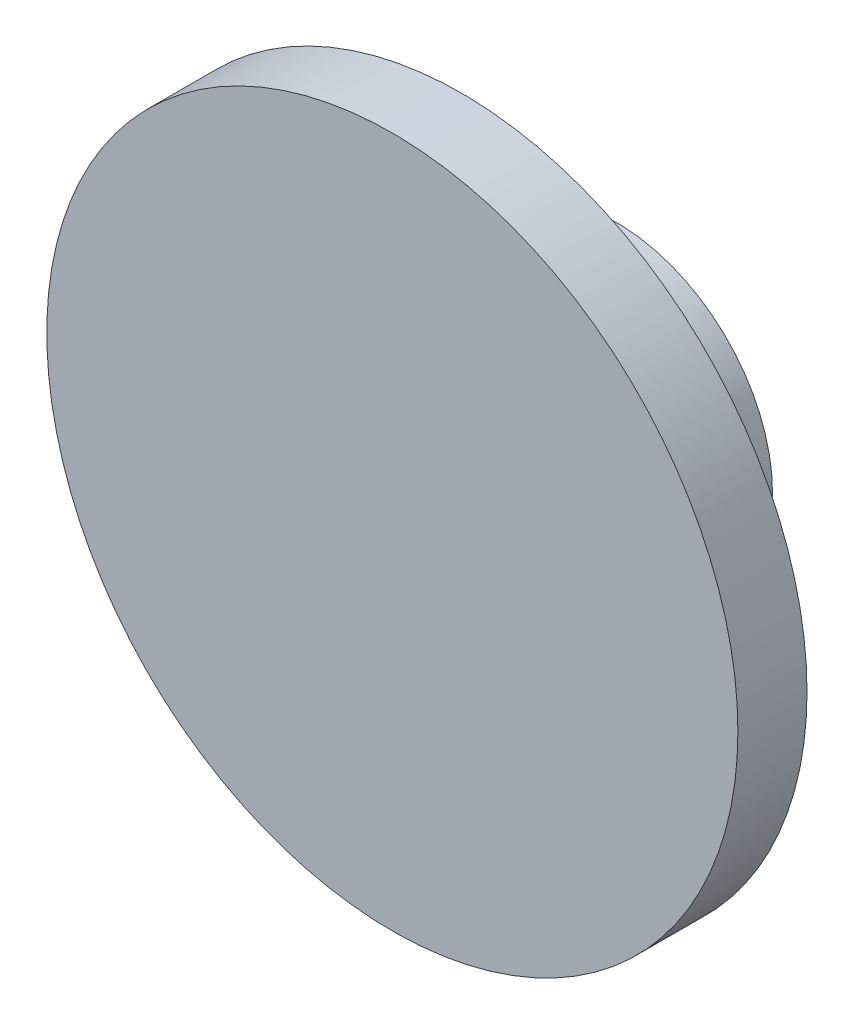
SolidWorks part; units mm, degrees
ref_plane "Front Plane" through (0, 0, 0) normal (0, 0, 1) x (1, 0, 0)
ref_plane "Top Plane" through (0, 0, 0) normal (0, 1, 0) x (1, 0, 0)
ref_plane "Right Plane" through (0, 0, 0) normal (1, 0, 0) x (0, 0, -1)
sketch "Sketch1" plane through (0, 0, 0) normal (0, 0, 1) x (1, 0, 0)
  circle A0 centre (0, 0) radius 4.5
  circle A1 centre (0, 0) radius 3.75
  dimension "D1" = 9
  dimension "D2" = 7.5
extrude "Boss-Extrude1" add sketch "Sketch1" along normal blind 4.5
sketch "Sketch2" plane through (0, 0, 4.5) normal (0, 0, 1) x (1, 0, 0)
  circle A0 centre (0, 0) radius 10
  dimension "D1" = 20
extrude "Boss-Extrude2" add sketch "Sketch2" along normal blind 2
